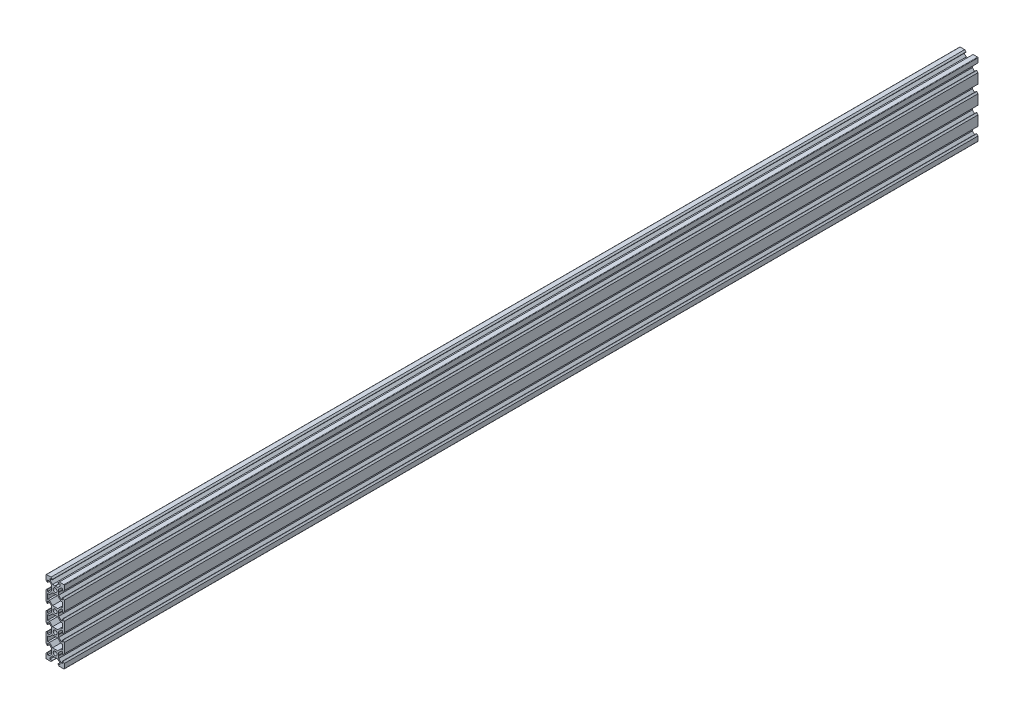
SolidWorks part; units mm, degrees
material "6061-T6 (SS)"
ref_plane "Front Plane" through (0, 0, 0) normal (0, 0, 1) x (1, 0, 0)
ref_plane "Top Plane" through (0, 0, 0) normal (0, 1, 0) x (1, 0, 0)
ref_plane "Right Plane" through (0, 0, 0) normal (1, 0, 0) x (0, 0, -1)
sketch "Sketch1" plane through (0, 0, 0) normal (0, 0, 1) x (1, 0, 0)
  line L0 (0, 0) -> (10, 0) construction
  line L1 (9.5, -40) -> (-9.5, -40)
  line L2 (10, -39.5) -> (10, 39.5)
  line L3 (9.5, 40) -> (-9.5, 40)
  line L4 (-10, -39.5) -> (-10, 39.5)
  line L5 (10, -40) -> (-10, 40) construction
  line L6 (10, 40) -> (-10, -40) construction
  circle A0 centre (0, 30) radius 2.1
  circle A1 centre (0, 10) radius 2.1
  circle A2 centre (0, -10) radius 2.1
  circle A3 centre (0, -30) radius 2.1
  arc A4 (-9.5, -40) -> (-10, -39.5) centre (-9.5, -39.5) cw
  arc A5 (9.5, -40) -> (10, -39.5) centre (9.5, -39.5) ccw
  arc A6 (10, 39.5) -> (9.5, 40) centre (9.5, 39.5) ccw
  arc A7 (-9.5, 40) -> (-10, 39.5) centre (-9.5, 39.5) ccw
  point P0 (0, 0)
  line B0 (0, 30) -> (0, 40) construction
  line B1 (0, 33.69) -> (-0.21, 33.9)
  line B2 (-0.21, 33.9) -> (-2.8393, 33.9)
  line B3 (-2.8393, 33.9) -> (-5.5, 36.5607)
  line B4 (-5.5, 36.5607) -> (-5.5, 38.2)
  line B5 (-5.5, 38.2) -> (-3.125, 38.2)
  line B6 (-3.125, 38.2) -> (-3.125, 38.545)
  line B7 (-3.125, 38.545) -> (-4.58, 40)
  line B8 (-4.58, 40) -> (4.58, 40)
  line B9 (0, 30) -> (-5.9132, 35.9132) construction
  line B10 (3.125, 38.545) -> (4.58, 40)
  line B11 (3.125, 38.2) -> (3.125, 38.545)
  line B12 (5.5, 38.2) -> (3.125, 38.2)
  line B13 (5.5, 36.5607) -> (5.5, 38.2)
  line B14 (2.8393, 33.9) -> (5.5, 36.5607)
  line B15 (0.21, 33.9) -> (2.8393, 33.9)
  line B16 (0, 33.69) -> (0.21, 33.9)
  line B17 (0, 30) -> (-10, 30) construction
  line B18 (-3.69, 30) -> (-3.9, 29.79)
  line B19 (-3.9, 29.79) -> (-3.9, 27.1607)
  line B20 (-3.9, 27.1607) -> (-6.5607, 24.5)
  line B21 (-6.5607, 24.5) -> (-8.2, 24.5)
  line B22 (-8.2, 24.5) -> (-8.2, 26.875)
  line B23 (-8.2, 26.875) -> (-8.545, 26.875)
  line B24 (-8.545, 26.875) -> (-10, 25.42)
  line B25 (-10, 25.42) -> (-10, 34.58)
  line B26 (0, 30) -> (-5.9132, 24.0868) construction
  line B27 (-8.545, 33.125) -> (-10, 34.58)
  line B28 (-8.2, 33.125) -> (-8.545, 33.125)
  line B29 (-8.2, 35.5) -> (-8.2, 33.125)
  line B30 (-6.5607, 35.5) -> (-8.2, 35.5)
  line B31 (-3.9, 32.8393) -> (-6.5607, 35.5)
  line B32 (-3.9, 30.21) -> (-3.9, 32.8393)
  line B33 (-3.69, 30) -> (-3.9, 30.21)
  line B34 (0, 10) -> (-10, 10) construction
  line B35 (-3.69, 10) -> (-3.9, 9.79)
  line B36 (-3.9, 9.79) -> (-3.9, 7.1607)
  line B37 (-3.9, 7.1607) -> (-6.5607, 4.5)
  line B38 (-6.5607, 4.5) -> (-8.2, 4.5)
  line B39 (-8.2, 4.5) -> (-8.2, 6.875)
  line B40 (-8.2, 6.875) -> (-8.545, 6.875)
  line B41 (-8.545, 6.875) -> (-10, 5.42)
  line B42 (-10, 5.42) -> (-10, 14.58)
  line B43 (0, 10) -> (-5.9132, 4.0868) construction
  line B44 (-8.545, 13.125) -> (-10, 14.58)
  line B45 (-8.2, 13.125) -> (-8.545, 13.125)
  line B46 (-8.2, 15.5) -> (-8.2, 13.125)
  line B47 (-6.5607, 15.5) -> (-8.2, 15.5)
  line B48 (-3.9, 12.8393) -> (-6.5607, 15.5)
  line B49 (-3.9, 10.21) -> (-3.9, 12.8393)
  line B50 (-3.69, 10) -> (-3.9, 10.21)
  line B51 (0, -10) -> (-10, -10) construction
  line B52 (-3.69, -10) -> (-3.9, -10.21)
  line B53 (-3.9, -10.21) -> (-3.9, -12.8393)
  line B54 (-3.9, -12.8393) -> (-6.5607, -15.5)
  line B55 (-6.5607, -15.5) -> (-8.2, -15.5)
  line B56 (-8.2, -15.5) -> (-8.2, -13.125)
  line B57 (-8.2, -13.125) -> (-8.545, -13.125)
  line B58 (-8.545, -13.125) -> (-10, -14.58)
  line B59 (-10, -14.58) -> (-10, -5.42)
  line B60 (0, -10) -> (-5.9132, -15.9132) construction
  line B61 (-8.545, -6.875) -> (-10, -5.42)
  line B62 (-8.2, -6.875) -> (-8.545, -6.875)
  line B63 (-8.2, -4.5) -> (-8.2, -6.875)
  line B64 (-6.5607, -4.5) -> (-8.2, -4.5)
  line B65 (-3.9, -7.1607) -> (-6.5607, -4.5)
  line B66 (-3.9, -9.79) -> (-3.9, -7.1607)
  line B67 (-3.69, -10) -> (-3.9, -9.79)
  line B68 (0, -30) -> (-10, -30) construction
  line B69 (-3.69, -30) -> (-3.9, -30.21)
  line B70 (-3.9, -30.21) -> (-3.9, -32.8393)
  line B71 (-3.9, -32.8393) -> (-6.5607, -35.5)
  line B72 (-6.5607, -35.5) -> (-8.2, -35.5)
  line B73 (-8.2, -35.5) -> (-8.2, -33.125)
  line B74 (-8.2, -33.125) -> (-8.545, -33.125)
  line B75 (-8.545, -33.125) -> (-10, -34.58)
  line B76 (-10, -34.58) -> (-10, -25.42)
  line B77 (0, -30) -> (-5.9132, -35.9132) construction
  line B78 (-8.545, -26.875) -> (-10, -25.42)
  line B79 (-8.2, -26.875) -> (-8.545, -26.875)
  line B80 (-8.2, -24.5) -> (-8.2, -26.875)
  line B81 (-6.5607, -24.5) -> (-8.2, -24.5)
  line B82 (-3.9, -27.1607) -> (-6.5607, -24.5)
  line B83 (-3.9, -29.79) -> (-3.9, -27.1607)
  line B84 (-3.69, -30) -> (-3.9, -29.79)
  line B85 (0, -30) -> (0, -40) construction
  line B86 (0, -33.69) -> (0.21, -33.9)
  line B87 (0.21, -33.9) -> (2.8393, -33.9)
  line B88 (2.8393, -33.9) -> (5.5, -36.5607)
  line B89 (5.5, -36.5607) -> (5.5, -38.2)
  line B90 (5.5, -38.2) -> (3.125, -38.2)
  line B91 (3.125, -38.2) -> (3.125, -38.545)
  line B92 (3.125, -38.545) -> (4.58, -40)
  line B93 (4.58, -40) -> (-4.58, -40)
  line B94 (0, -30) -> (5.9132, -35.9132) construction
  line B95 (-3.125, -38.545) -> (-4.58, -40)
  line B96 (-3.125, -38.2) -> (-3.125, -38.545)
  line B97 (-5.5, -38.2) -> (-3.125, -38.2)
  line B98 (-5.5, -36.5607) -> (-5.5, -38.2)
  line B99 (-2.8393, -33.9) -> (-5.5, -36.5607)
  line B100 (-0.21, -33.9) -> (-2.8393, -33.9)
  line B101 (0, -33.69) -> (-0.21, -33.9)
  line B102 (0, -30) -> (10, -30) construction
  line B103 (3.69, -30) -> (3.9, -29.79)
  line B104 (3.9, -29.79) -> (3.9, -27.1607)
  line B105 (3.9, -27.1607) -> (6.5607, -24.5)
  line B106 (6.5607, -24.5) -> (8.2, -24.5)
  line B107 (8.2, -24.5) -> (8.2, -26.875)
  line B108 (8.2, -26.875) -> (8.545, -26.875)
  line B109 (8.545, -26.875) -> (10, -25.42)
  line B110 (10, -25.42) -> (10, -34.58)
  line B111 (0, -30) -> (5.9132, -24.0868) construction
  line B112 (8.545, -33.125) -> (10, -34.58)
  line B113 (8.2, -33.125) -> (8.545, -33.125)
  line B114 (8.2, -35.5) -> (8.2, -33.125)
  line B115 (6.5607, -35.5) -> (8.2, -35.5)
  line B116 (3.9, -32.8393) -> (6.5607, -35.5)
  line B117 (3.9, -30.21) -> (3.9, -32.8393)
  line B118 (3.69, -30) -> (3.9, -30.21)
  line B119 (0, -10) -> (10, -10) construction
  line B120 (3.69, -10) -> (3.9, -9.79)
  line B121 (3.9, -9.79) -> (3.9, -7.1607)
  line B122 (3.9, -7.1607) -> (6.5607, -4.5)
  line B123 (6.5607, -4.5) -> (8.2, -4.5)
  line B124 (8.2, -4.5) -> (8.2, -6.875)
  line B125 (8.2, -6.875) -> (8.545, -6.875)
  line B126 (8.545, -6.875) -> (10, -5.42)
  line B127 (10, -5.42) -> (10, -14.58)
  line B128 (0, -10) -> (5.9132, -4.0868) construction
  line B129 (8.545, -13.125) -> (10, -14.58)
  line B130 (8.2, -13.125) -> (8.545, -13.125)
  line B131 (8.2, -15.5) -> (8.2, -13.125)
  line B132 (6.5607, -15.5) -> (8.2, -15.5)
  line B133 (3.9, -12.8393) -> (6.5607, -15.5)
  line B134 (3.9, -10.21) -> (3.9, -12.8393)
  line B135 (3.69, -10) -> (3.9, -10.21)
  line B136 (0, 10) -> (10, 10) construction
  line B137 (3.69, 10) -> (3.9, 10.21)
  line B138 (3.9, 10.21) -> (3.9, 12.8393)
  line B139 (3.9, 12.8393) -> (6.5607, 15.5)
  line B140 (6.5607, 15.5) -> (8.2, 15.5)
  line B141 (8.2, 15.5) -> (8.2, 13.125)
  line B142 (8.2, 13.125) -> (8.545, 13.125)
  line B143 (8.545, 13.125) -> (10, 14.58)
  line B144 (10, 14.58) -> (10, 5.42)
  line B145 (0, 10) -> (5.9132, 15.9132) construction
  line B146 (8.545, 6.875) -> (10, 5.42)
  line B147 (8.2, 6.875) -> (8.545, 6.875)
  line B148 (8.2, 4.5) -> (8.2, 6.875)
  line B149 (6.5607, 4.5) -> (8.2, 4.5)
  line B150 (3.9, 7.1607) -> (6.5607, 4.5)
  line B151 (3.9, 9.79) -> (3.9, 7.1607)
  line B152 (3.69, 10) -> (3.9, 9.79)
  line B153 (0, 30) -> (10, 30) construction
  line B154 (3.69, 30) -> (3.9, 30.21)
  line B155 (3.9, 30.21) -> (3.9, 32.8393)
  line B156 (3.9, 32.8393) -> (6.5607, 35.5)
  line B157 (6.5607, 35.5) -> (8.2, 35.5)
  line B158 (8.2, 35.5) -> (8.2, 33.125)
  line B159 (8.2, 33.125) -> (8.545, 33.125)
  line B160 (8.545, 33.125) -> (10, 34.58)
  line B161 (10, 34.58) -> (10, 25.42)
  line B162 (0, 30) -> (5.9132, 35.9132) construction
  line B163 (8.545, 26.875) -> (10, 25.42)
  line B164 (8.2, 26.875) -> (8.545, 26.875)
  line B165 (8.2, 24.5) -> (8.2, 26.875)
  line B166 (6.5607, 24.5) -> (8.2, 24.5)
  line B167 (3.9, 27.1607) -> (6.5607, 24.5)
  line B168 (3.9, 29.79) -> (3.9, 27.1607)
  line B169 (3.69, 30) -> (3.9, 29.79)
  line B170 (-8.2, 17.3) -> (-8.2, 22.7)
  line B171 (-8.2, 22.7) -> (-6.2393, 22.7)
  line B172 (-6.2393, 22.7) -> (-2.8393, 26.1)
  line B173 (-2.8393, 26.1) -> (2.8393, 26.1)
  line B174 (0, 26.1) -> (0, 20) construction
  line B175 (0, 20) -> (-8.2, 20) construction
  line B176 (6.2393, 22.7) -> (2.8393, 26.1)
  line B177 (8.2, 22.7) -> (6.2393, 22.7)
  line B178 (8.2, 17.3) -> (8.2, 22.7)
  line B179 (8.2, 17.3) -> (6.2393, 17.3)
  line B180 (6.2393, 17.3) -> (2.8393, 13.9)
  line B181 (-2.8393, 13.9) -> (2.8393, 13.9)
  line B182 (-6.2393, 17.3) -> (-2.8393, 13.9)
  line B183 (-8.2, 17.3) -> (-6.2393, 17.3)
  line B184 (0, 26.1) -> (0, 30) construction
  line B185 (0, 30) -> (-5.0927, 24.9073) construction
  line B186 (-8.2, -2.7) -> (-8.2, 2.7)
  line B187 (-8.2, 2.7) -> (-6.2393, 2.7)
  line B188 (-6.2393, 2.7) -> (-2.8393, 6.1)
  line B189 (-2.8393, 6.1) -> (2.8393, 6.1)
  line B190 (0, 6.1) -> (0, 0) construction
  line B191 (0, 0) -> (-8.2, 0) construction
  line B192 (6.2393, 2.7) -> (2.8393, 6.1)
  line B193 (8.2, 2.7) -> (6.2393, 2.7)
  line B194 (8.2, -2.7) -> (8.2, 2.7)
  line B195 (8.2, -2.7) -> (6.2393, -2.7)
  line B196 (6.2393, -2.7) -> (2.8393, -6.1)
  line B197 (-2.8393, -6.1) -> (2.8393, -6.1)
  line B198 (-6.2393, -2.7) -> (-2.8393, -6.1)
  line B199 (-8.2, -2.7) -> (-6.2393, -2.7)
  line B200 (0, 6.1) -> (0, 10) construction
  line B201 (0, 10) -> (-5.0927, 4.9073) construction
  line B202 (-8.2, -22.7) -> (-8.2, -17.3)
  line B203 (-8.2, -17.3) -> (-6.2393, -17.3)
  line B204 (-6.2393, -17.3) -> (-2.8393, -13.9)
  line B205 (-2.8393, -13.9) -> (2.8393, -13.9)
  line B206 (0, -13.9) -> (0, -20) construction
  line B207 (0, -20) -> (-8.2, -20) construction
  line B208 (6.2393, -17.3) -> (2.8393, -13.9)
  line B209 (8.2, -17.3) -> (6.2393, -17.3)
  line B210 (8.2, -22.7) -> (8.2, -17.3)
  line B211 (8.2, -22.7) -> (6.2393, -22.7)
  line B212 (6.2393, -22.7) -> (2.8393, -26.1)
  line B213 (-2.8393, -26.1) -> (2.8393, -26.1)
  line B214 (-6.2393, -22.7) -> (-2.8393, -26.1)
  line B215 (-8.2, -22.7) -> (-6.2393, -22.7)
  line B216 (0, -13.9) -> (0, -10) construction
  line B217 (0, -10) -> (-5.0927, -15.0927) construction
  dimension "D5" = 4.2
  dimension "D6" = 0.5
  dimension "D1" = 20
  dimension "D2" = 80
  dimension "D3" = 20
  dimension "D4" = 20
sketch_block_instance "V Slot 1-4"
sketch_block "V Slot 1" parameters "D1"=10, "D2"=11, "D3"=4.3, "D4"=1.8, "D5"=0.21, "D6"=45, "D7"=9.16, "D8"=1.5, "D9"=6.25
sketch_block_instance "V Slot 1-5"
sketch_block_instance "V Slot 1-6"
sketch_block_instance "V Slot 1-7"
sketch_block_instance "V Slot 1-8"
sketch_block_instance "V Slot 1-9"
sketch_block_instance "V Slot 1-10"
sketch_block_instance "V Slot 1-11"
sketch_block_instance "V Slot 1-12"
sketch_block_instance "V Slot 1-13"
sketch_block_instance "Center Cutout 1-1"
sketch_block "Center Cutout 1" parameters "D1"=5.4, "D2"=12.2, "D3"=8.2, "D4"=45, "D5"=10, "D6"=1.5
sketch_block_instance "Center Cutout 1-2"
sketch_block_instance "Center Cutout 1-3"
extrude "Boss-Extrude1" add sketch "Sketch1" along normal blind 1000 contours B169 B154 B155 B156 B157 B158 B159 B160 L2 A6 L3 B10 B11 B12 B13 B14 B15 B16 B1 B2 B3 B4 B5 B6 B7 A7 L4 B27 B28 B29 B30 B31 B32 B33 B18 B19 B20 B21 B22 B23 B24 B44 B45 B46 B47 B48 B49 B50 B35
